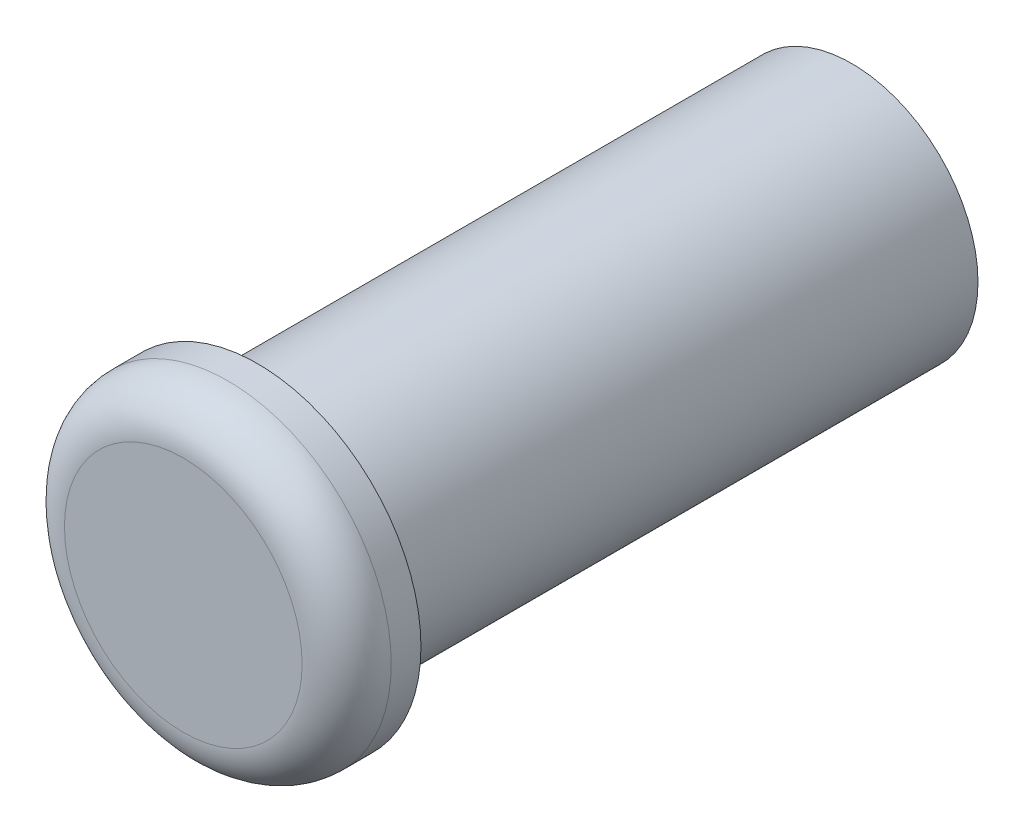
SolidWorks part; units mm, degrees
ref_plane "Front Plane" through (0, 0, 0) normal (0, 0, 1) x (1, 0, 0)
ref_plane "Top Plane" through (0, 0, 0) normal (0, 1, 0) x (1, 0, 0)
ref_plane "Right Plane" through (0, 0, 0) normal (1, 0, 0) x (0, 0, -1)
sketch "Sketch1" plane through (0, 0, 0) normal (0, 0, 1) x (1, 0, 0)
  circle A0 centre (0, 0) radius 8.5
  dimension "D1" = 17
extrude "Boss-Extrude1" add sketch "Sketch1" along normal blind 40
sketch "Sketch2" plane through (0, 0, 40) normal (0, 0, 1) x (1, 0, 0)
  circle A0 centre (0, 0) radius 11
  dimension "D1" = 22
extrude "Boss-Extrude2" add sketch "Sketch2" along normal blind 5
fillet "Fillet1" radius 3 1 edges at (11, 0, 45)
